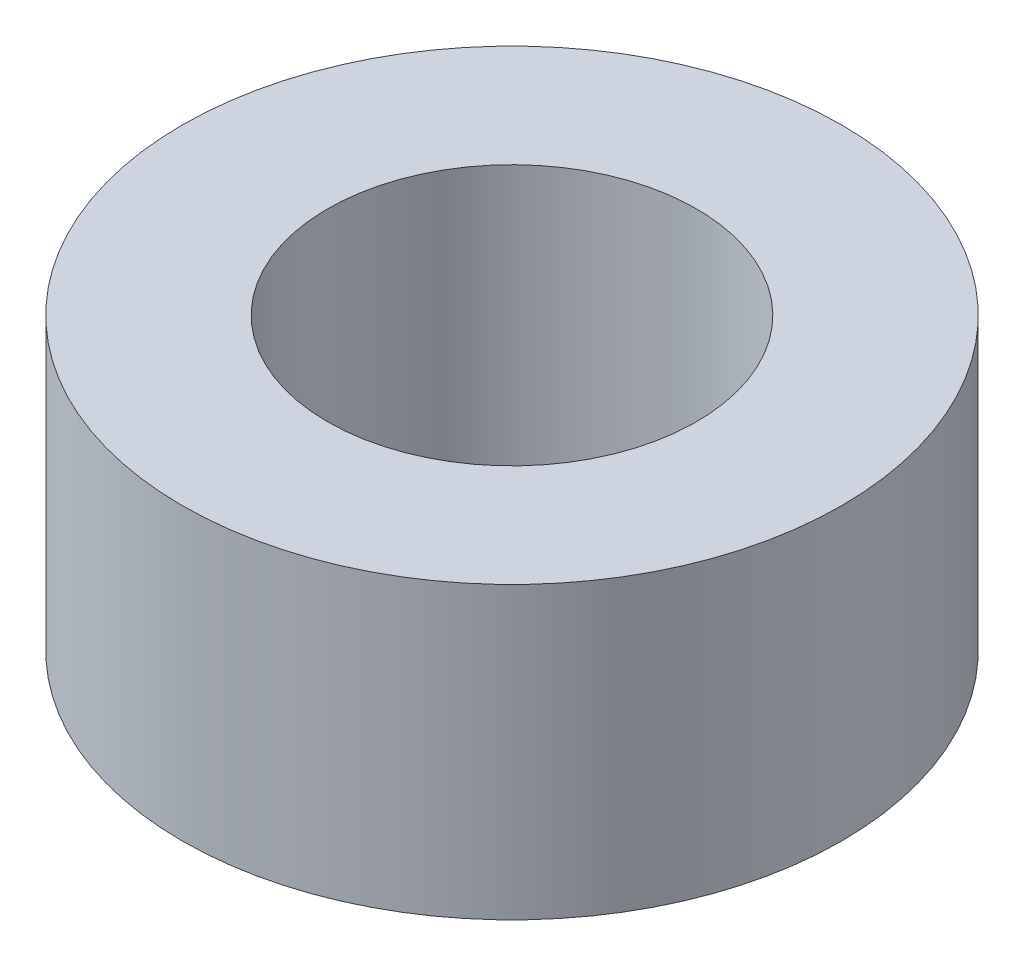
SolidWorks part; units mm, degrees
ref_plane "Front Plane" through (0, 0, 0) normal (0, 0, 1) x (1, 0, 0)
ref_plane "Top Plane" through (0, 0, 0) normal (0, 1, 0) x (1, 0, 0)
ref_plane "Right Plane" through (0, 0, 0) normal (1, 0, 0) x (0, 0, -1)
sketch "Sketch1" plane through (0, 0, 0) normal (0, 1, 0) x (1, 0, 0)
  circle A0 centre (0, 0) radius 6.35
  circle A1 centre (0, 0) radius 11.35
  dimension "D1" = 12.7
  dimension "D2" = 5
extrude "Boss-Extrude1" add sketch "Sketch1" along normal blind 10
